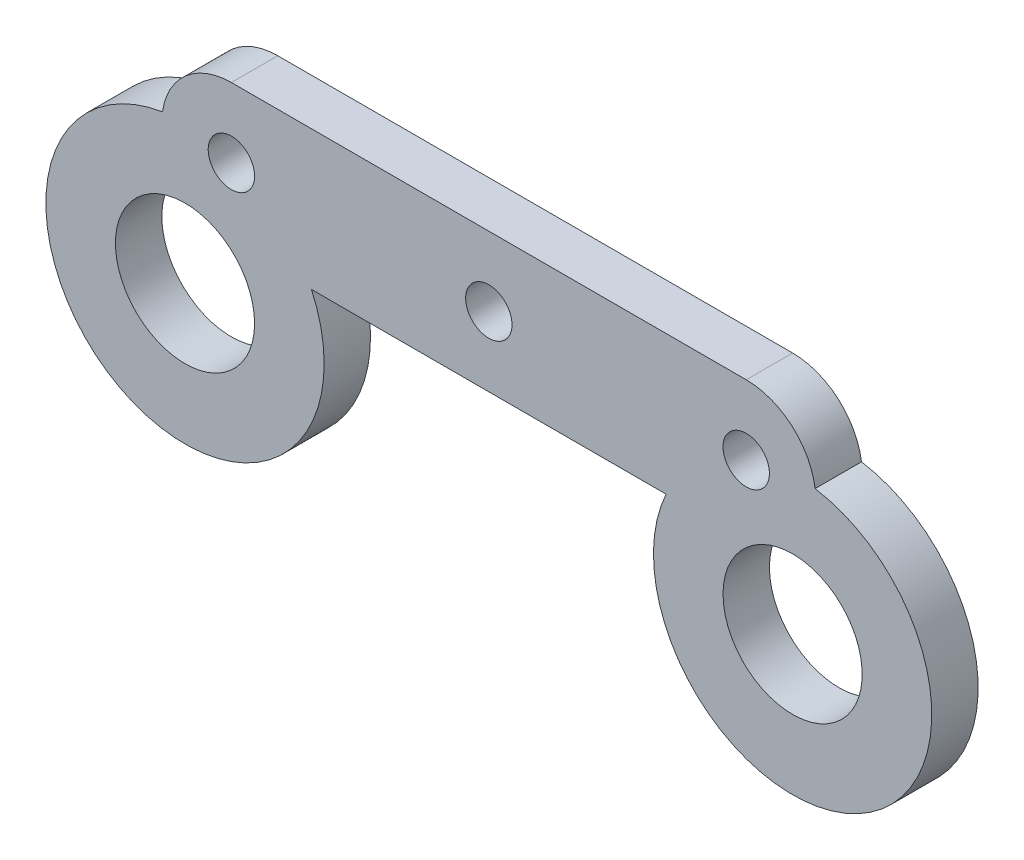
SolidWorks part; units mm, degrees
ref_plane "Front Plane" through (0, 0, 0) normal (0, 0, 1) x (1, 0, 0)
ref_plane "Top Plane" through (0, 0, 0) normal (0, 1, 0) x (1, 0, 0)
ref_plane "Right Plane" through (0, 0, 0) normal (1, 0, 0) x (0, 0, -1)
sketch "Sketch1" plane through (0, 0, 0) normal (0, 0, 1) x (1, 0, 0)
  line L2 (-11.1002, 3) -> (11.1002, 3)
  line L3 (-7.6458, -3) -> (7.6458, -3)
  circle A0 centre (0, 0) radius 1
  circle A4 centre (-13.1002, -5.5) radius 3
  circle A5 centre (13.1002, -5.5) radius 3
  arc A9 (14.0705, 0.421) -> (11.1002, 3) centre (11.1002, 0) ccw
  circle A13 centre (-11.1002, 0) radius 1
  arc A14 (-11.1002, 3) -> (-14.0705, 0.421) centre (-11.1002, 0) ccw
  circle A15 centre (11.1002, 0) radius 1
  arc A16 (-14.0705, 0.421) -> (-7.6458, -3) centre (-13.1002, -5.5) ccw
  arc A18 (7.6458, -3) -> (14.0705, 0.421) centre (13.1002, -5.5) ccw
  dimension "D3" = 6
  dimension "D4" = 7.6458
  dimension "D5" = 11.1002
  dimension "D6" = 13.1002
  dimension "D2" = 2
  dimension "D1" = 6
  dimension "D7" = 7.6458
extrude "Boss-Extrude1" add sketch "Sketch1" along normal blind 2
sketch "Sketch2" plane through (0, -3, 0) normal (0, -1, 0) x (1, 0, 0)
  line L0 (7.6458, 2) -> (7.6458, 0) construction
  line L1 (-7.6458, 0) -> (7.6458, 0) construction
  circle A0 centre (0, 1) radius 0.5
  dimension "D1" = 1
  dimension "D2" = 7.6458
  dimension "D3" = 1
extrude "Cut-Extrude1" cut sketch "Sketch2" against normal blind 0.5
